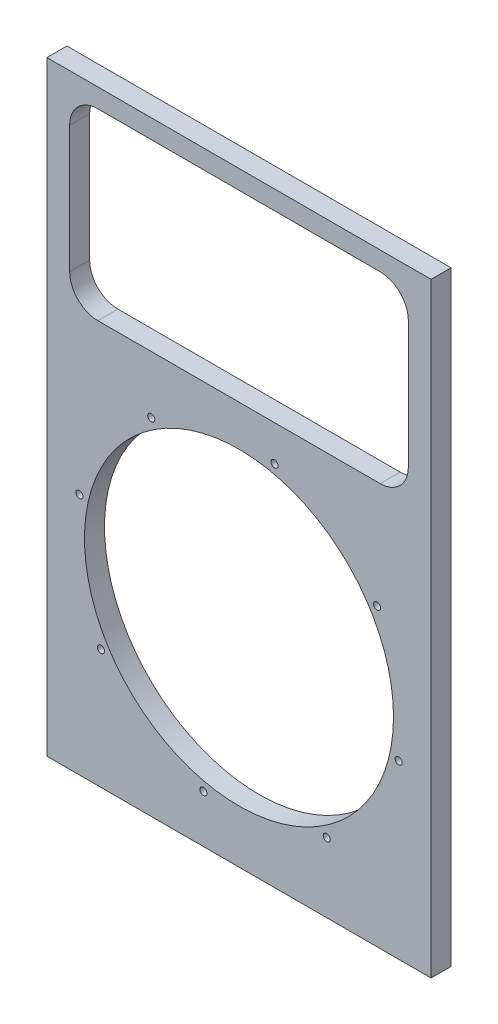
SolidWorks part; units mm, degrees
ref_plane "Front Plane" through (0, 0, 0) normal (0, 0, 1) x (1, 0, 0)
ref_plane "Top Plane" through (0, 0, 0) normal (0, 1, 0) x (1, 0, 0)
ref_plane "Right Plane" through (0, 0, 0) normal (1, 0, 0) x (0, 0, -1)
sketch "Sketch1" plane through (0, 0, 0) normal (0, 0, 1) x (1, 0, 0)
  line L1 (0, 0) -> (345.7, 0)
  line L2 (0, 0) -> (0, 544.6)
  line L3 (0, 544.6) -> (345.7, 544.6)
  line L4 (345.7, 0) -> (345.7, 544.6)
  dimension "D1" = 345.7
  dimension "D2" = 544.6
extrude "Boss-Extrude1" add sketch "Sketch1" along normal blind 18
sketch "Sketch2" plane through (0, 0, 18) normal (0, 0, 1) x (1, 0, 0)
  line L0 (0, 0) -> (345.7, 0) construction
  line L1 (39.5, 508.5) -> (306.2, 508.5)
  line L2 (39.5, 508.5) -> (39.5, 381.5)
  line L3 (39.5, 381.5) -> (306.2, 381.5)
  line L4 (306.2, 508.5) -> (306.2, 381.5)
  line L5 (345.7, 544.6) -> (0, 544.6) construction
  point P4 (306.2, 445)
  point P7 (172.85, 508.5)
  point P10 (172.85, 544.6)
  dimension "D1" = 445
  dimension "D2" = 127
  dimension "D3" = 266.7
  dimension "D4" = 0
extrude "Cut-Extrude1" cut sketch "Sketch2" against normal through all
sketch "Sketch3" plane through (0, 0, 18) normal (0, 0, 1) x (1, 0, 0)
  line L0 (39.5, 381.5) -> (306.2, 381.5) construction
  circle A0 centre (172.85, 186.691) radius 139.065
  point P4 (172.85, 381.5)
  dimension "D2" = 278.13
  dimension "D1" = 0
extrude "Cut-Extrude2" cut sketch "Sketch3" against normal through all
sketch "Sketch4" plane through (0, 0, 18) normal (0, 0, 1) x (1, 0, 0)
  circle A1 centre (204.8422, 330.3652) radius 3.175
  circle A2 centre (297.0649, 265.6621) radius 3.175
  circle A3 centre (316.5242, 154.6988) radius 3.175
  circle A4 centre (251.8211, 62.4761) radius 3.175
  circle A5 centre (140.8578, 43.0167) radius 3.175
  circle A6 centre (48.6351, 107.7198) radius 3.175
  circle A7 centre (29.1758, 218.6831) radius 3.175
  circle A8 centre (93.8789, 310.9059) radius 3.175
  point P20 (172.85, 186.691)
  dimension "D2" = 6.35
  dimension "D3" = 8
extrude "Cut-Extrude3" cut sketch "Sketch4" against normal through all
sketch "Sketch6" plane through (0, 0, 18) normal (0, 0, 1) x (1, 0, 0)
  line L0 (39.5, 508.5) -> (39.5, 381.5) construction
  line L1 (45.85, 362.45) -> (299.85, 362.45)
  line L2 (20.45, 387.85) -> (20.45, 502.15)
  line L3 (45.85, 527.55) -> (299.85, 527.55)
  line L4 (325.25, 387.85) -> (325.25, 502.15)
  line L5 (306.2, 508.5) -> (39.5, 508.5) construction
  arc A0 (45.85, 362.45) -> (20.45, 387.85) centre (45.85, 387.85) cw
  arc A1 (299.85, 362.45) -> (325.25, 387.85) centre (299.85, 387.85) ccw
  arc A2 (299.85, 527.55) -> (325.25, 502.15) centre (299.85, 502.15) cw
  arc A3 (20.45, 502.15) -> (45.85, 527.55) centre (45.85, 502.15) cw
  point P4 (39.5, 445)
  point P7 (20.45, 445)
  point P8 (172.85, 508.5)
  point P11 (172.85, 527.55)
  point P14 (20.45, 362.45)
  point P19 (325.25, 527.55)
  point P22 (20.45, 527.55)
  dimension "D5" = 25.4
  dimension "D1" = 304.8
  dimension "D2" = 165.1
  dimension "D3" = 0
  dimension "D4" = 0
extrude "Cut-Extrude4" cut sketch "Sketch6" against normal through all
